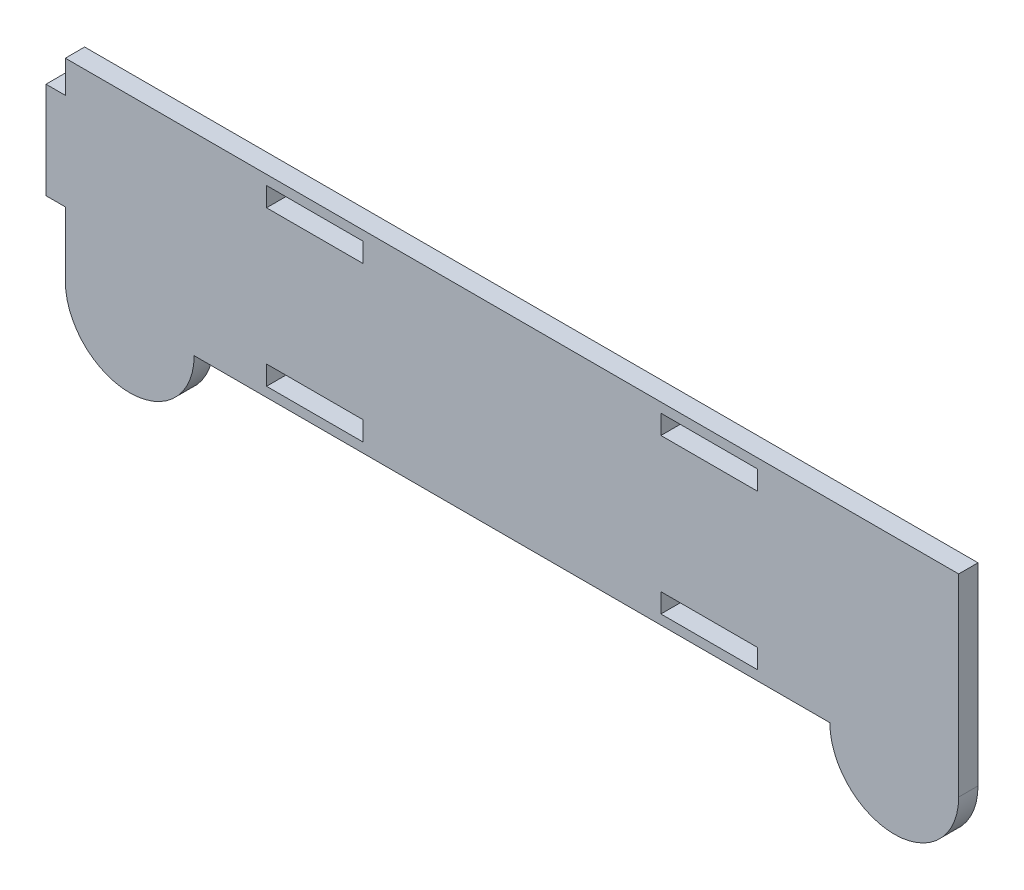
SolidWorks part; units mm, degrees
ref_plane "Front Plane" through (0, 0, 0) normal (0, 0, 1) x (1, 0, 0)
ref_plane "Top Plane" through (0, 0, 0) normal (0, 1, 0) x (1, 0, 0)
ref_plane "Right Plane" through (0, 0, 0) normal (1, 0, 0) x (0, 0, -1)
sketch "Sketch1" plane through (0, 0, 0) normal (0, 0, 1) x (1, 0, 0)
  line L0 (138.7, 8.9591) -> (138.7, 38.9591)
  line L1 (20, 8.9591) -> (118.7, 8.9591)
  line L2 (0, 38.9591) -> (0, 33.9591)
  line L3 (0, 38.9591) -> (138.7, 38.9591)
  line L4 (0, 33.9591) -> (-3, 33.9591)
  line L5 (-3, 33.9591) -> (-3, 18.9591)
  line L6 (-3, 18.9591) -> (0, 18.9591)
  line L7 (0, 18.9591) -> (0, 8.9591)
  arc A0 (0, 8.9591) -> (20, 8.9591) centre (10, 8.9591) ccw
  arc A1 (138.7, 8.9591) -> (118.7, 8.9591) centre (128.7, 8.9591) cw
  point P5 (138.7, 8.9591)
  point P6 (0, 8.9591)
  dimension "D5" = 10
  dimension "D6" = 10
  dimension "D1" = 138.7
  dimension "D2" = 30
  dimension "D3" = 15
  dimension "D4" = 20
  dimension "D7" = 20
  dimension "D8" = 30
  dimension "D9" = 3
  dimension "D10" = 5
  dimension "D11" = 3
extrude "Boss-Extrude1" add sketch "Sketch1" along normal blind 3
sketch "Sketch2" plane through (0, 0, 3) normal (0, 0, 1) x (1, 0, 0)
  line L0 (138.7, 38.9591) -> (0, 38.9591) construction
  line L1 (31.24, 37.4591) -> (46.24, 37.4591)
  line L2 (31.24, 37.4591) -> (31.24, 34.4591)
  line L3 (31.24, 34.4591) -> (46.24, 34.4591)
  line L4 (46.24, 37.4591) -> (46.24, 34.4591)
  line L5 (92.47, 37.4591) -> (107.47, 37.4591)
  line L6 (92.47, 37.4591) -> (92.47, 34.4591)
  line L7 (92.47, 34.4591) -> (107.47, 34.4591)
  line L8 (107.47, 37.4591) -> (107.47, 34.4591)
  line L10 (138.7, 8.9591) -> (138.7, 38.9591) construction
  line L11 (20, 8.9591) -> (118.7, 8.9591) construction
  line L12 (31.24, 13.4591) -> (46.24, 13.4591)
  line L13 (31.24, 13.4591) -> (31.24, 10.4591)
  line L14 (31.24, 10.4591) -> (46.24, 10.4591)
  line L15 (46.24, 13.4591) -> (46.24, 10.4591)
  line L16 (92.47, 13.4591) -> (107.47, 13.4591)
  line L17 (92.47, 13.4591) -> (92.47, 10.4591)
  line L18 (92.47, 10.4591) -> (107.47, 10.4591)
  line L19 (107.47, 13.4591) -> (107.47, 10.4591)
  dimension "D1" = 15
  dimension "D2" = 15
  dimension "D3" = 3
  dimension "D4" = 3
  dimension "D5" = 1.5
  dimension "D6" = 1.5
  dimension "D7" = 46.23
  dimension "D8" = 31.23
  dimension "D9" = 1.5
  dimension "D10" = 1.5
  dimension "D11" = 15
  dimension "D12" = 15
  dimension "D13" = 3
  dimension "D14" = 3
  dimension "D15" = 46.23
  dimension "D16" = 31.23
extrude "Cut-Extrude1" cut sketch "Sketch2" against normal through all
equation "\"t\"=3"
equation "\"ws\"=15"
equation "\"wb\"=15"
equation "\"D3@Sketch1\"=\"wb\""
equation "\"D9@Sketch1\"=\"t\""
equation "\"D11@Sketch1\"=\"t\""
equation "\"D1@Sketch2\" = \"ws\""
equation "\"D2@Sketch2\"=\"ws\""
equation "\"D3@Sketch2\"=\"t\""
equation "\"D4@Sketch2\"=\"t\""
equation "\"D11@Sketch2\"=\"wb\""
equation "\"D12@Sketch2\"=\"wb\""
equation "\"D13@Sketch2\"=\"t\""
equation "\"D14@Sketch2\"=\"t\""
